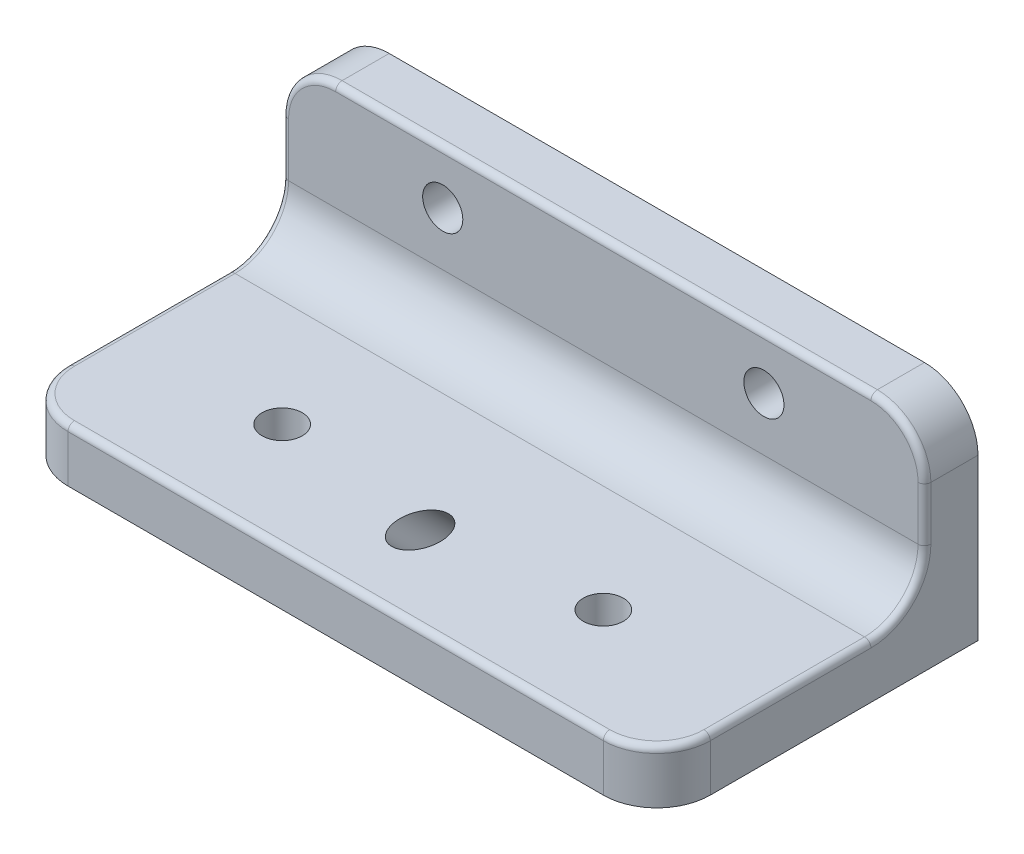
SolidWorks part; units mm, degrees
ref_plane "Front Plane" through (0, 0, 0) normal (0, 0, 1) x (1, 0, 0)
ref_plane "Top Plane" through (0, 0, 0) normal (0, 1, 0) x (1, 0, 0)
ref_plane "Right Plane" through (0, 0, 0) normal (1, 0, 0) x (0, 0, -1)
sketch "Sketch1" plane through (0, 0, 0) normal (0, 0, 1) x (1, 0, 0)
  line L0 (19.05, -12.7) -> (19.05, 8.798) construction
  line L1 (0, 0) -> (38.1, 0)
  line L2 (0, 0) -> (0, -12.7)
  line L3 (0, -12.7) -> (38.1, -12.7)
  line L4 (38.1, 0) -> (38.1, -12.7)
  circle A0 centre (9.525, -3.175) radius 1.1906
  circle A1 centre (28.575, -3.175) radius 1.1906
  dimension "D3" = 2.3813
  dimension "D1" = 38.1
  dimension "D2" = 12.7
  dimension "D4" = 9.525
  dimension "D5" = 9.525
extrude "Boss-Extrude1" add sketch "Sketch1" along normal blind 3.175
ref_plane "Plane1" through (0, -12.7, 0) normal (0, -1, 0) x (-1, 0, 0)
sketch "Sketch2" plane through (0, -12.7, 0) normal (0, -1, 0) x (-1, 0, 0)
  line L1 (0, -3.175) -> (-38.1, -3.175)
  line L2 (0, -3.175) -> (0, -19.05)
  line L3 (0, -19.05) -> (-38.1, -19.05)
  line L4 (-38.1, -3.175) -> (-38.1, -19.05)
  dimension "D1" = 15.875
extrude "Boss-Extrude2" add sketch "Sketch2" against normal blind 3.175
fillet "Fillet1" radius 3.175 5 edges at (38.1, 0, 1.5875) (0, 0, 1.5875) (38.1, -11.1125, 19.05) (0, -11.1125, 19.05)
fillet "Fillet2" radius 0.381 12 edges at (37.1701, -9.525, 18.1201) (38.1, -8.5951, 4.1049) (37.1701, -0.9299, 3.175) (19.05, 0, 3.175) (0.9299, -0.9299, 3.175) (0, -8.5951, 4.1049) (0.9299, -9.525, 18.1201) (19.05, -9.525, 19.05)
ref_plane "Plane2" through (0, 4.6509, 4.6509) normal (0, 0.7071, 0.7071) x (-1, 0, 0)
sketch "Sketch3" plane through (0, 4.6509, 4.6509) normal (0, 0.7071, 0.7071) x (-1, 0, 0)
  line L0 (0, 18.2299) -> (0, 11.4947) construction
  line L1 (-34.925, 20.475) -> (-3.175, 20.475) construction
  circle A0 centre (-19.05, 16.665) radius 1.1906
  dimension "D1" = 2.3813
  dimension "D2" = 19.05
  dimension "D3" = 3.81
extrude "Cut-Extrude1" cut sketch "Sketch3" against normal through all
sketch "Sketch4" plane through (0, -12.7, 0) normal (0, -1, 0) x (-1, 0, 0)
  line L0 (-34.925, -19.05) -> (-3.175, -19.05) construction
  line L1 (0, -15.875) -> (0, 0) construction
  line L2 (-19.05, -19.05) -> (-19.05, 8.5813) construction
  circle A0 centre (-9.525, -12.7) radius 1.1906
  circle A1 centre (-28.575, -12.7) radius 1.1906
  dimension "D1" = 2.3813
  dimension "D2" = 6.35
  dimension "D3" = 9.525
extrude "Cut-Extrude2" cut sketch "Sketch4" against normal through all
